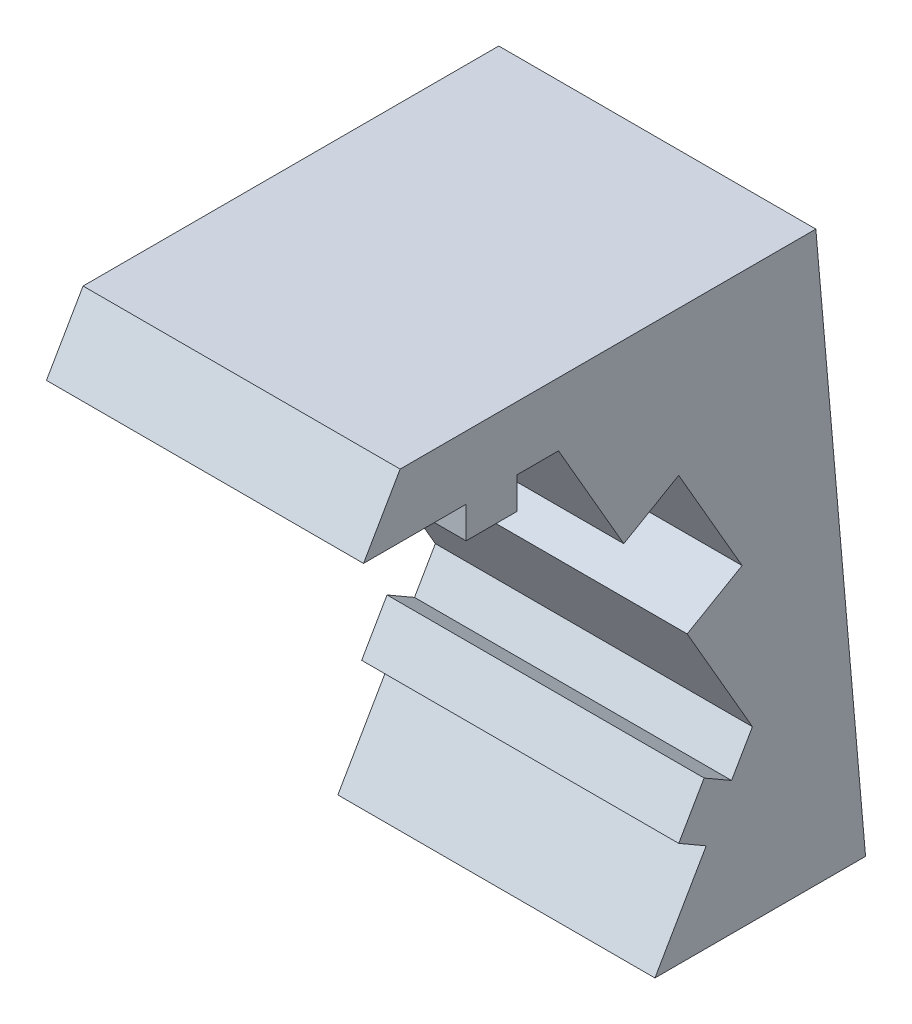
SolidWorks part; units mm, degrees
ref_plane "Front Plane" through (0, 0, 0) normal (0, 0, 1) x (1, 0, 0)
ref_plane "Top Plane" through (0, 0, 0) normal (0, 1, 0) x (1, 0, 0)
ref_plane "Right Plane" through (0, 0, 0) normal (1, 0, 0) x (0, 0, -1)
sketch "Sketch1" plane through (50.25, 0, 0) normal (1, 0, 0) x (0, 0, -1)
  line L0 (9.1561, -5.3258) -> (10.7732, -2.5249)
  line L1 (10.7732, -2.5249) -> (9.9072, -2.0249)
  line L2 (9.9072, -2.0249) -> (10.7072, -0.6392)
  line L3 (10.7072, -0.6392) -> (11.5732, -1.1392)
  line L4 (11.5732, -1.1392) -> (12.2309, 0)
  line L5 (12.2309, 0) -> (10.1732, 3.5641)
  line L6 (6.1155, 10.5923) -> (4.8, 10.5923)
  line L7 (4.8, 10.5923) -> (4.8, 9.5923)
  line L8 (4.8, 9.5923) -> (3.2, 9.5923)
  line L9 (3.2, 9.5923) -> (3.2, 10.5923)
  line L10 (3.2, 10.5923) -> (-0.0343, 10.5923)
  line L26 (6, 10.3923) -> (5, 10.3923)
  line L27 (5, 10.3923) -> (5, 9.3923)
  line L28 (5, 9.3923) -> (3, 9.3923)
  line L29 (3, 9.3923) -> (3, 10.3923)
  line L30 (3, 10.3923) -> (2, 10.3923)
  line L31 (-6, 10.3923) -> (-12, 0)
  line L32 (-12, 0) -> (-8.9829, -5.2258)
  line L33 (-8.9829, -5.2258) -> (-4.7, 2.1923)
  line L34 (-4.7, 2.1923) -> (-4.7, 2.7923)
  line L35 (-4.7, 2.7923) -> (-6.1, 4.1923)
  line L36 (-6.1, 4.1923) -> (-6.1, 4.7923)
  line L37 (-6.1, 4.7923) -> (-5.1, 4.7923)
  line L38 (-5.1, 4.7923) -> (-5.1, 5.3923)
  line L39 (-5.1, 5.3923) -> (5.1, 5.3923)
  line L40 (5.1, 5.3923) -> (5.1, 4.7923)
  line L41 (5.1, 4.7923) -> (6.1, 4.7923)
  line L42 (6.1, 4.7923) -> (6.1, 4.1923)
  line L43 (6.1, 4.1923) -> (4.7, 2.7923)
  line L44 (4.7, 2.7923) -> (4.7, 2.1923)
  line L45 (4.7, 2.1923) -> (8.9829, -5.2258)
  line L46 (8.9829, -5.2258) -> (10.5, -2.5981)
  line L47 (10.5, -2.5981) -> (9.634, -2.0981)
  line L48 (9.634, -2.0981) -> (10.634, -0.366)
  line L49 (10.634, -0.366) -> (11.5, -0.866)
  line L50 (11.5, -0.866) -> (12, 0)
  line L51 (12, 0) -> (6, 10.3923)
  line L52 (6, 10.3923) -> (5, 10.3923) construction
  line L53 (5, 10.3923) -> (5, 9.3923) construction
  line L54 (5, 9.3923) -> (3, 9.3923) construction
  line L55 (3, 9.3923) -> (3, 10.3923) construction
  line L56 (3, 10.3923) -> (2, 10.3923) construction
  line L72 (8.9829, -5.2258) -> (10.5, -2.5981) construction
  line L73 (10.5, -2.5981) -> (9.634, -2.0981) construction
  line L74 (9.634, -2.0981) -> (10.634, -0.366) construction
  line L75 (10.634, -0.366) -> (11.5, -0.866) construction
  line L76 (11.5, -0.866) -> (12, 0) construction
  line L77 (12, 0) -> (6, 10.3923) construction
  line L115 (9.1561, -5.3258) -> (14.2309, -5.3258)
  line L116 (14.2309, -5.3258) -> (14.2309, 12.5923) construction
  line L117 (14.2309, 12.5923) -> (1.1204, 12.5923)
  line L118 (1.1204, 12.5923) -> (-0.0343, 10.5923)
  line L120 (3.2, 10.5923) -> (2, 10.5923) construction
  line L122 (14.2309, 12.5923) -> (15.7986, -5.3258)
  line L123 (15.7986, -5.3258) -> (14.2309, -5.3258)
  line L124 (9.9053, 8.0282) -> (11.9053, 4.5641)
  line L126 (9.9053, 8.0282) -> (8.1732, 7.0282)
  line L127 (11.9053, 4.5641) -> (10.1732, 3.5641)
  line L128 (8.1732, 7.0282) -> (6.1155, 10.5923)
  line L130 (12.2309, 0) -> (6.1155, 10.5923) construction
  line L215 (2, 10.3923) -> (2, 8.3923)
  line L216 (2, 10.3923) -> (2, 8.3923)
  line L217 (2, 8.3923) -> (-2, 8.3923)
  line L218 (2, 8.3923) -> (-2, 8.3923)
  line L219 (-2, 8.3923) -> (-2, 10.3923)
  line L220 (-2, 8.3923) -> (-2, 10.3923)
  line L221 (-2, 10.3923) -> (-6, 10.3923)
  line L222 (-2, 10.3923) -> (-6, 10.3923)
  point P26 (12.2309, 4.1156)
  point P42 (10.9053, 6.2962)
  point P44 (12, 4.4159)
  dimension "D3" = 2
  dimension "D4" = 2
  dimension "D5" = 5
  dimension "D6" = 2
  dimension "D7" = 4
  dimension "D1" = 0
  dimension "D2" = 0.2
extrude "Boss-Extrude1" add sketch "Sketch1" against normal blind 10 contours L128 L126 L124 L127 L5 L4 L3 L2 L1 L0 L115 L123 L122 L117 L118 L10 L9 L8 L7 L6
